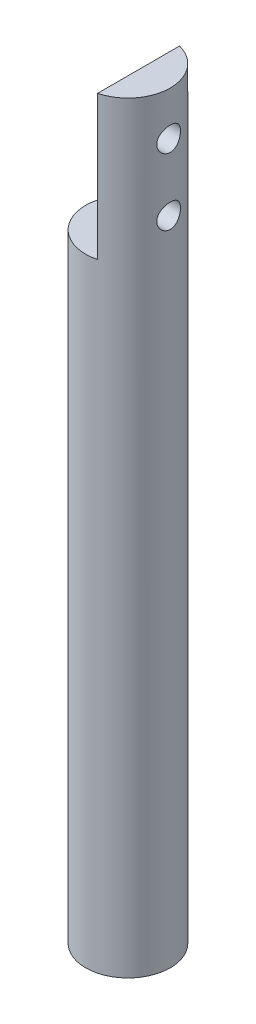
SolidWorks part; units mm, degrees
ref_plane "Front" through (0, 0, 0) normal (0, 0, 1) x (1, 0, 0)
ref_plane "Top" through (0, 0, 0) normal (0, 1, 0) x (1, 0, 0)
ref_plane "Right" through (0, 0, 0) normal (1, 0, 0) x (0, 0, -1)
sketch "草图1" plane through (0, 0, 0) normal (0, 1, 0) x (1, 0, 0)
  circle A0 centre (0, 0) radius 3.175
extrude "凸台-拉伸1" add sketch "草图1" along normal blind 57.15
sketch "草图2" plane through (0, 57.15, 0) normal (0, 1, 0) x (1, 0, 0)
  line L0 (0, 0) -> (0, 3.175) construction
  line L1 (-0.794, 3.175) -> (0.794, 3.175)
  line L2 (0.794, 3.175) -> (0.794, -3.175)
  line L3 (0.794, -3.175) -> (-3.175, -3.175)
  line L4 (-3.175, -3.175) -> (-3.175, 3.175)
  line L5 (-3.175, 3.175) -> (-0.794, 3.175)
  line L6 (0, 0) -> (0.794, 0) construction
  circle A0 centre (0, 0) radius 3.175 construction
  point P8 (0, 3.175)
extrude "切除-拉伸1" cut sketch "草图2" against normal blind 10.795
sketch "草图3" plane through (0.794, 0, 0) normal (-1, 0, 0) x (0, 0, 1)
  line L0 (0, 57.15) -> (0, 53.855) construction
  line L1 (3.0741, 57.15) -> (-3.0741, 57.15) construction
  line L2 (0, 57.15) -> (0, 48.855) construction
  line L3 (0, 53.855) -> (0, 57.15) construction
  circle A0 centre (0, 53.855) radius 0.889
  circle A1 centre (0, 48.855) radius 0.889
extrude "切除-拉伸2" cut sketch "草图3" against normal blind 10.795
sketch "草图4" plane through (0, 0, 0) normal (0, -1, 0) x (1, 0, 0)
  line L0 (0, 0) -> (-3.175, 0) construction
  line L1 (-3.175, 0) -> (0, 0) construction
  line L2 (0, 0) -> (0, -3.175) construction
  line L3 (0, -3.175) -> (0, -1.5875) construction
  line L4 (0, -1.5875) -> (0, -2.3813) construction
  line L5 (0, -2.3813) -> (-1.9811, -2.3813) construction
  line L6 (-1.9811, -2.3813) -> (1.9451, -2.3813) construction
  line L7 (-1.9811, -2.3813) -> (1.9451, -2.3813)
  line L8 (1.9451, -2.3813) -> (1.9451, -3.175)
  line L9 (1.9451, -3.175) -> (-1.9811, -3.175)
  line L10 (-1.9811, -3.175) -> (-1.9811, -2.3813)
  circle A0 centre (0, 0) radius 3.175 construction
extrude "切除-拉伸3" cut sketch "草图4" against normal blind 8.573
